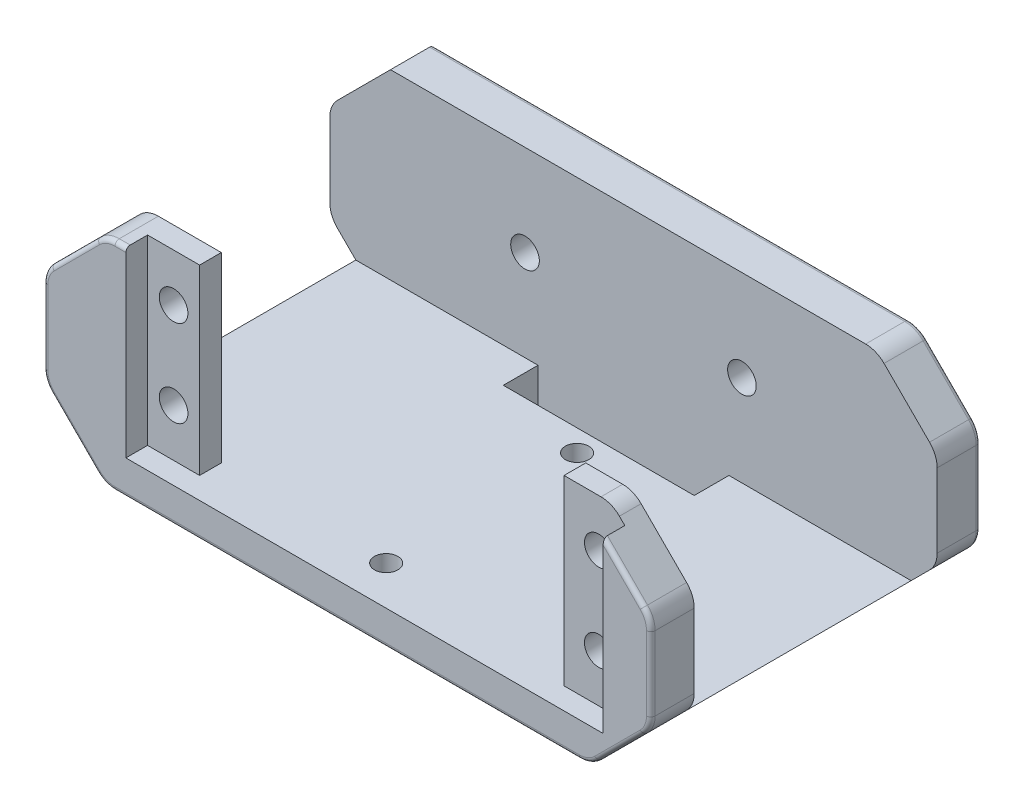
SolidWorks part; units mm, degrees
ref_plane "前视基准面" through (0, 0, 0) normal (0, 0, 1) x (1, 0, 0)
ref_plane "上视基准面" through (0, 0, 0) normal (0, 1, 0) x (1, 0, 0)
ref_plane "右视基准面" through (0, 0, 0) normal (1, 0, 0) x (0, 0, -1)
sketch "草图1" plane through (0, 0, 0) normal (0, 0, 1) x (1, 0, 0)
  line L0 (7, 0) -> (63, 0)
  line L1 (70, 7) -> (70, 18)
  line L2 (63, 25) -> (7, 25)
  line L3 (0, 18) -> (0, 7)
  line L4 (0, 7) -> (7, 0)
  line L5 (7, 25) -> (0, 18)
  line L6 (70, 18) -> (63, 25)
  line L7 (63, 0) -> (70, 7)
  point P0 (0, 0)
  point P1 (70, 0)
  point P4 (70, 25)
  point P5 (0, 25)
  dimension "D1" = 70
  dimension "D2" = 25
extrude "凸台-拉伸1" add sketch "草图1" along normal blind 38
sketch "草图2" plane through (0, 25, 0) normal (0, 1, 0) x (1, 0, 0)
  line L0 (0, -38) -> (0, 0) construction
  line L1 (0, -5) -> (70, -5)
  line L2 (0, -5) -> (0, -33)
  line L3 (0, -33) -> (70, -33)
  line L4 (70, -5) -> (70, -33)
  line L5 (70, -38) -> (70, 0) construction
  line L6 (63, 0) -> (7, 0) construction
  line L8 (63, -38) -> (7, -38) construction
  dimension "D1" = 5
  dimension "D2" = 5
extrude "切除-拉伸1" cut sketch "草图2" against normal offset from surface (21 mm away) 4 up to face at (35, 0, 19)
sketch "草图3" plane through (0, 0, 38) normal (0, 0, 1) x (1, 0, 0)
  line L0 (63, 25) -> (7, 25) construction
  line L1 (15.5, 25) -> (57.5, 25)
  line L2 (15.5, 25) -> (15.5, 4)
  line L3 (15.5, 4) -> (57.5, 4)
  line L4 (57.5, 25) -> (57.5, 4)
  line L5 (7, 0) -> (63, 0) construction
  line L6 (0, 18) -> (0, 7) construction
  line L7 (70, 7) -> (70, 18) construction
  circle A0 centre (12.5, 19.5) radius 1.65
  circle A1 centre (12.5, 9.5) radius 1.65
  circle A2 centre (61.5, 19.5) radius 1.65
  circle A3 centre (61.5, 9.5) radius 1.65
  dimension "D4" = 3.3
  dimension "D5" = 3.3
  dimension "D6" = 3.3
  dimension "D7" = 3.3
  dimension "D1" = 4
  dimension "D2" = 15.5
  dimension "D3" = 12.5
  dimension "D8" = 3
  dimension "D9" = 5.5
  dimension "D10" = 10
  dimension "D11" = 4
extrude "切除-拉伸2" cut sketch "草图3" against normal blind 20
sketch "草图5" plane through (0, 0, 0) normal (0, 0, -1) x (-1, 0, 0)
  circle A4 centre (-22.5, 14.5) radius 1.65
  circle A5 centre (-47.5, 14.5) radius 1.65
  dimension "D5" = 3.3
  dimension "D6" = 3.3
extrude "切除-拉伸3" cut sketch "草图5" against normal blind 10
sketch "草图7" plane through (0, 0, 38) normal (0, 0, 1) x (1, 0, 0)
  line L0 (70, 7) -> (70, 18) construction
  line L1 (64.5, 29.5155) -> (9.5, 29.5155)
  line L2 (64.5, 29.5155) -> (64.5, 4)
  line L3 (64.5, 4) -> (9.5, 4)
  line L4 (9.5, 29.5155) -> (9.5, 4)
  line L6 (0, 18) -> (0, 7) construction
  line L7 (15.5, 4) -> (57.5, 4) construction
  point P6 (64.5, 25.6914)
  dimension "D1" = 5.5
  dimension "D3" = 9.5
extrude "切除-拉伸4" cut sketch "草图7" against normal blind 2.5
fillet "圆角1" radius 3 13 edges at (63, 25, 34.25) (63, 25, 2.5) (70, 18, 2.5) (70, 18, 35.5) (70, 7, 35.5) (70, 7, 2.5) (63, 0, 19) (0, 18, 2.5) (0, 7, 2.5) (7, 25, 35.5) (0, 18, 35.5) (0, 7, 35.5) (7, 0, 19)
fillet "圆角2" radius 0.5 30 edges at (8.8713, 25, 38) (7.0946, 24.7716, 38) (3.5, 21.5, 38) (0.2284, 17.9054, 38) (0, 12.5, 38) (0.2284, 7.0946, 38) (66.8107, 21.1893, 38) (69.7716, 17.9054, 38) (70, 12.5, 38) (69.7716, 7.0946, 38) (66.5, 3.5, 38) (62.9054, 0.2284, 38) (35, 0, 38) (7.0946, 0.2284, 38) (3.9393, 21.9393, 0) (0.2284, 17.9054, 0) (0, 12.5, 0) (0.2284, 7.0946, 0) (3.5, 3.5, 0) (7.0946, 0.2284, 0) (34.3787, 25, 0) (62.9054, 24.7716, 0) (66.5, 21.5, 0) (69.7716, 17.9054, 0) (70, 12.5, 0) (69.7716, 7.0946, 0) (66.5, 3.5, 0) (62.9054, 0.2284, 0) (3.5, 3.5, 38) (35, 0, 0)
sketch "草图8" plane through (0, 4, 0) normal (0, 1, 0) x (1, 0, 0)
  line L0 (3, -5) -> (67, -5) construction
  line L1 (24, -5) -> (46, -5)
  line L2 (24, -5) -> (24, -9)
  line L3 (24, -9) -> (46, -9)
  line L4 (46, -5) -> (46, -9)
  circle A0 centre (35, -11.5) radius 1.35
  circle A1 centre (35, -33.5) radius 1.35
  point P9 (35, -5)
  point P15 (35, -5)
  point P17 (35, -9)
  dimension "D5" = 2.7
  dimension "D6" = 2.7
  dimension "D1" = 4
  dimension "D2" = 22
  dimension "D3" = 6.5
  dimension "D4" = 22
extrude "切除-拉伸5" cut sketch "草图8" against normal through all
